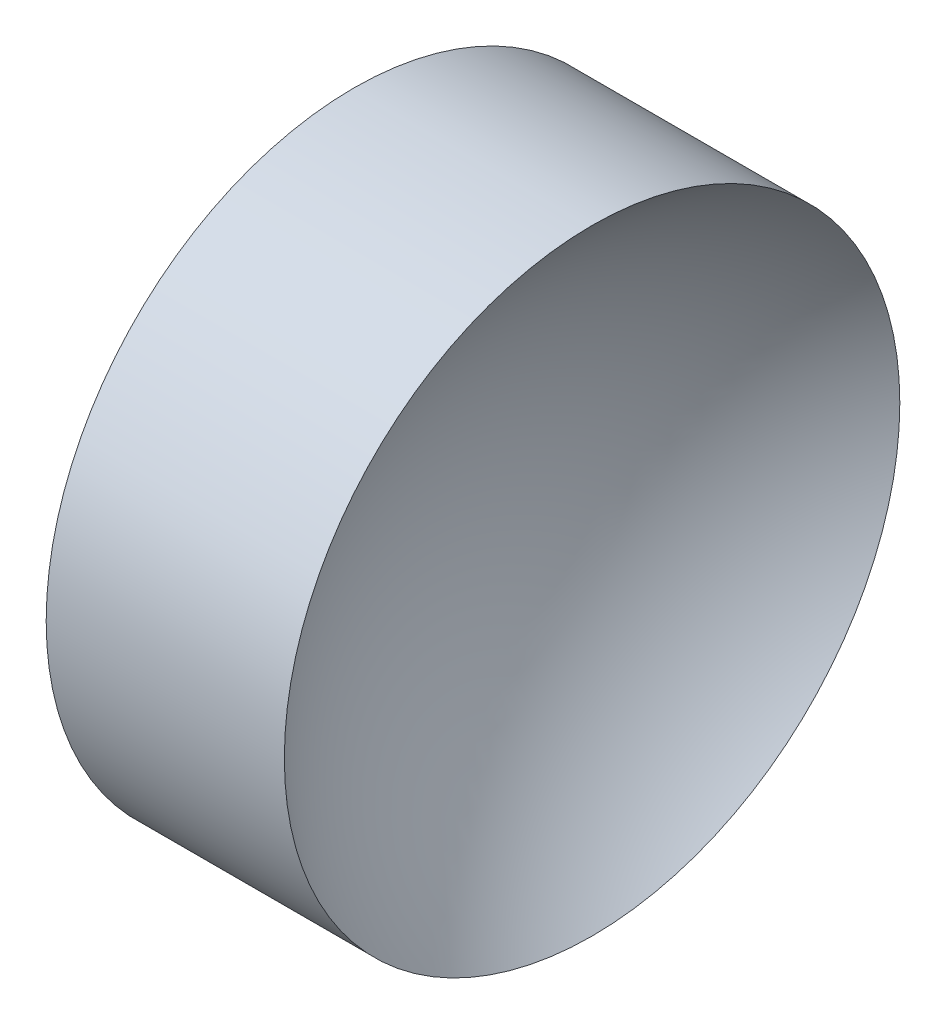
SolidWorks part; units mm, degrees
ref_plane "前视基准面" through (0, 0, 0) normal (0, 0, 1) x (1, 0, 0)
ref_plane "上视基准面" through (0, 0, 0) normal (0, 1, 0) x (1, 0, 0)
ref_plane "右视基准面" through (0, 0, 0) normal (1, 0, 0) x (0, 0, -1)
sketch "草图1" plane through (0, 0, 0) normal (0, 0, 1) x (1, 0, 0)
  line L0 (21.506, 13.0311) -> (26.997, 13.0311) construction
  line L1 (22.4242, 13.0311) -> (22.4242, 18.0311)
  line L2 (22.4242, 18.0311) -> (26.2938, 18.0311)
  line L3 (23.9242, 13.0311) -> (22.4242, 13.0311)
  arc A0 (26.2938, 18.0311) -> (23.9242, 13.0311) centre (30.3842, 13.0311) ccw
revolve "旋转1" add sketch "草图1" angle 360 about L0
